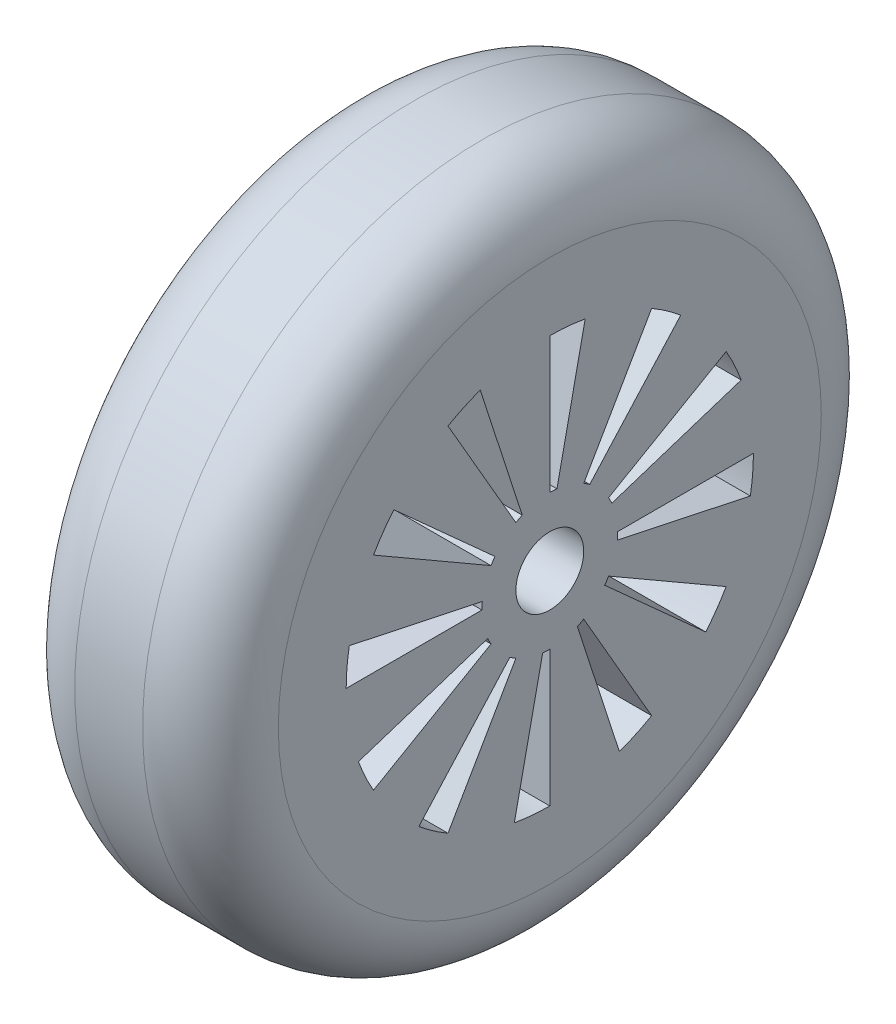
SolidWorks part; units mm, degrees
ref_plane "Front Plane" through (0, 0, 0) normal (0, 0, 1) x (1, 0, 0)
ref_plane "Top Plane" through (0, 0, 0) normal (0, 1, 0) x (1, 0, 0)
ref_plane "Right Plane" through (0, 0, 0) normal (1, 0, 0) x (0, 0, -1)
sketch "Sketch1" plane through (0, 0, 0) normal (1, 0, 0) x (0, 0, -1)
  circle A1 centre (0, 0) radius 50
  dimension "D1" = 100
extrude "Boss-Extrude1" add sketch "Sketch1" along normal blind 30
sketch "Sketch2" plane through (30, 0, 0) normal (1, 0, 0) x (0, 0, -1)
  circle A0 centre (0, 0) radius 5
  dimension "D1" = 10
extrude "Cut-Extrude1" cut sketch "Sketch2" against normal through all
sketch "Sketch3" plane through (30, 0, 0) normal (1, 0, 0) x (0, 0, -1)
  line L0 (0, -5) -> (0, -30)
  line L1 (0, -5) -> (-5.2168, -29.5429)
  circle A1 centre (0, 0) radius 30
  circle A2 centre (0, 0) radius 5 construction
  circle A3 centre (0, 0) radius 10
  dimension "D1" = 60
  dimension "D2" = 20
  dimension "D3" = 12
extrude "Cut-Extrude10" cut sketch "Sketch3" against normal through all contours A3 L1 A1 L0
pattern_circular "CirPattern1" count 12 over 360 about axis through (0, 0, 0) along (1, 0, 0) of "Cut-Extrude10"
fillet "Fillet1" radius 10 2 edges at (0, 0, -50) (30, 0, -50)
